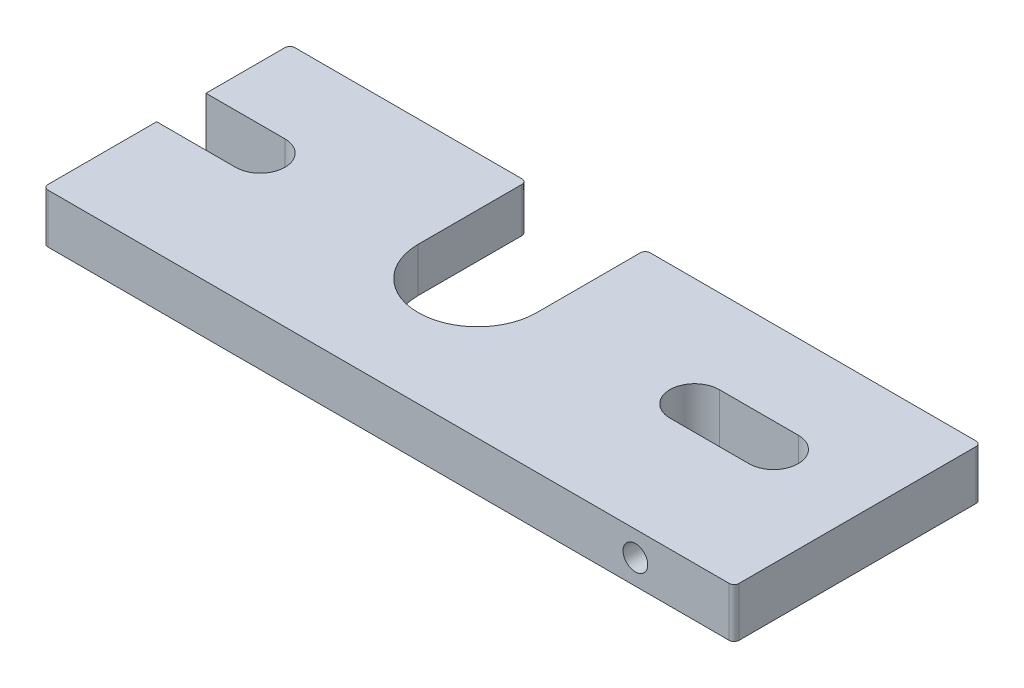
SolidWorks part; units mm, degrees
material "6061-T6 (SS)"
ref_plane "Front Plane" through (0, 0, 0) normal (0, 0, 1) x (1, 0, 0)
ref_plane "Top Plane" through (0, 0, 0) normal (0, 1, 0) x (1, 0, 0)
ref_plane "Right Plane" through (0, 0, 0) normal (1, 0, 0) x (0, 0, -1)
sketch "Sketch1" plane through (0, 0, 0) normal (0, 1, 0) x (1, 0, 0)
  line L0 (22, 2.5) -> (30, 2.5)
  line L1 (-30, 11) -> (-6, 11)
  line L2 (-30, 11) -> (-30, 2.5)
  line L3 (-30, -14) -> (40, -14)
  line L4 (40, 11) -> (40, -14)
  line L5 (30, -2.5) -> (22, -2.5)
  line L6 (-6, 0) -> (-6, 11)
  line L7 (6, 0) -> (6, 11)
  line L8 (-22, 2.5) -> (-30, 2.5)
  line L9 (-22, -2.5) -> (-30, -2.5)
  line L10 (-30, -2.5) -> (-30, -14)
  line L11 (6, 11) -> (40, 11)
  arc A0 (-6, 0) -> (6, 0) centre (0, 0) ccw
  arc A1 (-22, -2.5) -> (-22, 2.5) centre (-22, 0) ccw
  arc A2 (22, 2.5) -> (22, -2.5) centre (22, 0) ccw
  arc A3 (30, -2.5) -> (30, 2.5) centre (30, 0) ccw
  dimension "D1" = 12
  dimension "D2" = 11
  dimension "D3" = 25
  dimension "D4" = 70
  dimension "D5" = 5
  dimension "D6" = 22
  dimension "D7" = 8
  dimension "D8" = 22
  dimension "D9" = 24
extrude "Boss-Extrude1" add sketch "Sketch1" along normal blind 5
sketch "Sketch2" plane through (0, 0, 0) normal (0, -1, 0) x (1, 0, 0)
  line L0 (-9, 0) -> (-9, -11)
  line L1 (-6, -11) -> (-30, -11) construction
  line L2 (-9, -11) -> (9, -11)
  line L3 (40, -11) -> (6, -11) construction
  line L4 (9, -11) -> (9, 0)
  arc A0 (9, 0) -> (-9, 0) centre (0, 0) ccw
  dimension "D1" = 18
extrude "Cut-Extrude1" cut sketch "Sketch2" against normal blind 0.5
sketch "Sketch3" plane through (0, 0, 0) normal (0, -1, 0) x (1, 0, 0)
  line L0 (-14, 8) -> (-14, -5) construction
  line L1 (-11, 8) -> (-11, -5)
  line L2 (-17, 8) -> (-17, -5)
  line L3 (14.5, 8) -> (14.5, -5) construction
  line L4 (18, 8) -> (18, -5)
  line L5 (11, 8) -> (11, -5)
  line L6 (36.35, 7.5) -> (36.35, -5) construction
  line L7 (38.85, 7.5) -> (38.85, -5)
  line L8 (33.85, 7.5) -> (33.85, -5)
  line L9 (40, 14) -> (40, -11) construction
  line L10 (40, -11) -> (9, -11) construction
  line L11 (-30, 14) -> (40, 14) construction
  line L12 (-9, -11) -> (-30, -11) construction
  line L13 (6, 0) -> (6, -11) construction
  line L14 (-6, -11) -> (-6, 0) construction
  arc A0 (-11, 8) -> (-17, 8) centre (-14, 8) ccw
  arc A1 (-17, -5) -> (-11, -5) centre (-14, -5) ccw
  arc A2 (18, 8) -> (11, 8) centre (14.5, 8) ccw
  arc A3 (11, -5) -> (18, -5) centre (14.5, -5) ccw
  arc A4 (38.85, 7.5) -> (33.85, 7.5) centre (36.35, 7.5) ccw
  arc A5 (33.85, -5) -> (38.85, -5) centre (36.35, -5) ccw
  point P2 (-14, 1.5)
  point P7 (14.5, 1.5)
  point P14 (36.35, 1.25)
  dimension "D5" = 3.5
  dimension "D6" = 4
  dimension "D7" = 2.5
  dimension "D8" = 2.5
  dimension "D9" = 3
  dimension "D10" = 3
  dimension "D1" = 6
  dimension "D2" = 7
  dimension "D3" = 5
  dimension "D4" = 1.15
  dimension "D11" = 5
  dimension "D12" = 5
extrude "Cut-Extrude2" cut sketch "Sketch3" against normal blind 3
hole_wizard "M3x0.5 Tapped Hole1" positions "Sketch5" profile "Sketch4" tap size "M3x0.5" standard "Ansi Metric"
sketch "Sketch5" plane through (0, 0, 14) normal (0, 0, 1) x (1, 0, 0)
  line L0 (40, 5) -> (40, 0) construction
  line L1 (30, 2.5) -> (40, 2.5) construction
  point P0 (30, 2.5)
  dimension "D1" = 10
sketch "Sketch4" plane through (30, 2.5, 14) normal (1, 0, 0) x (0, -1, 0)
  line L0 (0, 0) -> (0, 8.2511)
  line L1 (0, 8.2511) -> (1.25, 7.5)
  line L2 (1.25, 7.5) -> (1.25, 0)
  line L5 (1.25, 0) -> (0, 0)
  line L10 (0, 8.2511) -> (-1.25, 7.5) construction
  line L11 (0, -6.35) -> (0, 107.95) construction
  dimension "Tap Drill Dia." = 2.5
  dimension "Tap Drill Depth" = 7.5
  dimension "Drill Angle" = 118
cosmetic thread "Hole Thread1" parameters "D1"=5, "D2"=3
fillet "Fillet1" radius 0.5 6 edges at (-6, 2.75, -11) (40, 2.5, -11) (40, 2.5, 14) (6, 2.75, -11) (-30, 2.5, 14) (-30, 2.5, -11)
